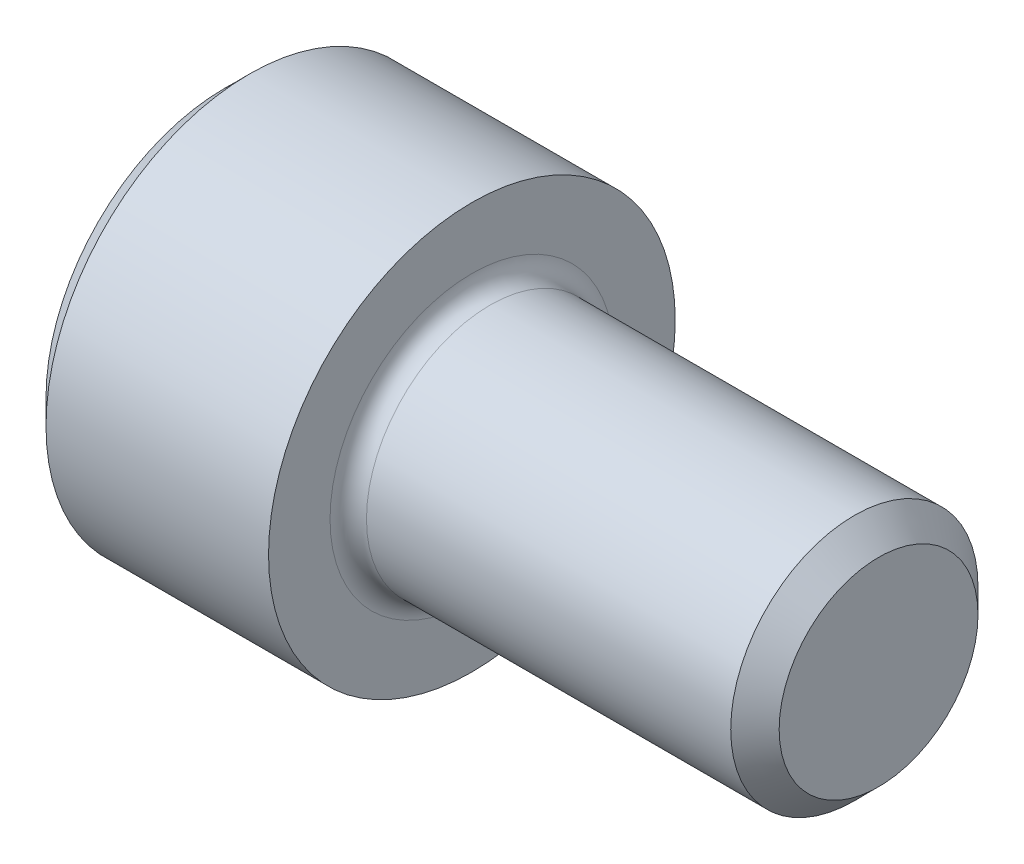
SolidWorks part; units mm, degrees
revolve "Base-Revolve" add sketch "BodySke"
sketch "BodySke" plane through (0, 0, 0) normal (0, 0, 1) x (1, 0, 0)
  line L0 (0, 0) -> (0, 3.4862)
  line L1 (0.4826, 3.9688) -> (4.826, 3.9688)
  line L2 (4.826, 3.9688) -> (4.826, 2.413)
  line L3 (4.826, 2.413) -> (12.2911, 2.413)
  line L4 (12.7635, 1.9406) -> (12.7635, 0)
  line L5 (12.7635, 0) -> (0, 0)
  line L6 (-31.75, 0) -> (127, 0) construction
  line L7 (0, 3.4862) -> (0.4826, 3.9688)
  line L8 (12.7635, 1.9406) -> (12.2911, 2.413)
  line L9 (0, -3.4862) -> (0.4826, -3.9688) construction
  line L10 (12.7635, -1.9406) -> (12.2911, -2.413) construction
  line L11 (5.6185, 9.525) -> (5.6185, 3.175) construction
  line L12 (4.826, 9.525) -> (4.826, 3.175) construction
  line L13 (-25.3365, 9.525) -> (-25.3365, 3.175) construction
  dimension "Diameter" = 4.826
  dimension "Head_ht" = 4.826
  dimension "Length" = 7.9375
  dimension "Body_ch_ang" = 45
  dimension "Head_dia" = 7.9375
  dimension "Head_ch_ang" = 45
  dimension "Head_side_ht" = 4.3434
  dimension "Minor_dia" = 3.8811
  dimension "Advance" = 0.7925
  dimension "Thread_nom" = 7.9375
  dimension "Thread_length" = 38.1
cosmetic thread "ThreadCosmetic" [suppressed]
fillet "Fillet1" radius 0.3556 1 edges at (4.826, 0, 2.413)
material "Plastique personnalisé"
ref_plane "Plane1" through (0, 0, 0) normal (0, 0, 1) x (1, 0, 0)
ref_plane "Plane2" through (0, 0, 0) normal (0, 1, 0) x (1, 0, 0)
ref_plane "Plane3" through (0, 0, 0) normal (1, 0, 0) x (0, 0, -1)
sketch "Sketch2" plane through (0, 0, 0) normal (0, 0, 1) x (1, 0, 0)
  line L0 (0, 1.985) -> (2.286, 1.985)
  line L1 (2.286, 1.985) -> (3.432, 0)
  line L2 (-31.75, 0) -> (127, 0) construction
  line L3 (3.432, 0) -> (0, 0)
  line L4 (0, 0) -> (0, 1.985)
  line L5 (0, 3.4862) -> (0, -3.4862) construction
  line L6 (0, 0) -> (47.625, 0) construction
  line L7 (4.826, -3.9688) -> (4.826, 3.9688) construction
  dimension "D1" = 1.985
  dimension "D2" = 60
revolve "Hex-PreBroach" cut sketch "Sketch2" angle 360 about L6
sketch "Sketch3" plane through (0, 0, 0) normal (-1, 0, 0) x (0, 0.5, 0.866)
  line L0 (1.146, 1.985) -> (-1.146, 1.985)
  line L1 (-1.146, 1.985) -> (-2.2921, 0)
  line L2 (1.146, 1.985) -> (2.2921, 0)
  line L3 (1.146, -1.985) -> (2.2921, 0)
  line L4 (1.146, -1.985) -> (-1.146, -1.985)
  line L5 (-1.146, -1.985) -> (-2.2921, 0)
  dimension "D1" = 1.985
  dimension "D2" = 1.985
  dimension "Hex_size" = 3.97
extrude "Hex" cut sketch "Sketch3" against normal blind 2.286
sketch "Sketch4" plane through (0, 0, 0) normal (-1, 0, 0) x (0, 0, 1)
  line L0 (0, 0) -> (2.3876, 0)
  line L1 (0, 0) -> (6.1484, 3.5498) construction
  line L2 (0, 0) -> (1.1938, 2.0677)
  line L3 (1.9883, 0.576) -> (2.2704, 0.7389)
  line L4 (1.493, 1.4339) -> (1.7751, 1.5968)
  arc A0 (1.9883, 0.576) -> (1.493, 1.4339) centre (0, 0) ccw
  arc A1 (2.3876, 0) -> (2.2704, 0.7389) centre (0, 0) ccw
  arc A2 (1.1938, 2.0677) -> (1.7751, 1.5968) centre (0, 0) cw
  dimension "D1" = 30
  dimension "D2" = 60
  dimension "Spline_p_dim" = 0.9906
  dimension "D3" = 0.4953
extrude "Spline" [suppressed] cut sketch "Sketch4" against normal blind 2.286
pattern_circular "CirPattern1" [suppressed] count 6 every 60
sketch "Sketch5" plane through (0, 0, 0) normal (0, 0, 1) x (1, 0, 0)
  line L0 (-31.75, 0) -> (127, 0) construction
  line L2 (0, 3.4862) -> (0, -3.4862) construction
  circle A0 centre (1.651, 0) radius 0.5906
  dimension "Drilled_hole_dia" = 1.1811
  dimension "Drilled_hole_loc" = 1.651
extrude "Hole" [suppressed] cut sketch "Sketch5" against normal through all and the other way through all
pattern_circular "Drilled-4" [suppressed] count 2 every 60
pattern_circular "Drilled-6" [suppressed] count 3 every 60
sketch "ThdSchSke" plane through (0, 0, 0) normal (0, 0, 1) x (1, 0, 0)
  line L0 (5.6185, -1.9406) -> (5.2877, -2.413)
  line L1 (5.6185, -1.9406) -> (5.9493, -2.413)
  line L2 (5.9493, -2.413) -> (5.9493, -3.0162)
  line L3 (-3.175, 0) -> (5.1513, 0) construction
  line L5 (5.9493, -3.0162) -> (5.2877, -3.0162)
  line L6 (5.2877, -3.0162) -> (5.2877, -2.413)
  line L7 (0, 3.4862) -> (0, -3.4862) construction
  dimension "Thread_minor" = 3.8811
  dimension "Diameter" = 4.826
  dimension "Start" = 5.6185
revolve "ThreadSchematic" [suppressed] cut sketch "ThdSchSke" angle 360 about L3
pattern_linear "ThdSchPat" [suppressed]
equation "\"D2@Sketch3\" = \"Hex_size@Sketch3\" / 2"
equation "\"D1@Sketch3\" = \"Hex_size@Sketch3\" / 2"
equation "\"D1@Sketch2\" = \"Hex_size@Sketch3\" / 2"
equation "\"D3@Sketch4\" = \"Spline_p_dim@Sketch4\" / 2"
equation "\"Thread_minor@ThreadCosmetic\"  =  \"Minor_dia@BodySke\""
equation "\"D2@CirPattern1\" = 360 / \"Num_teeth@CirPattern1\""
equation "\"Wall_thickness@Sketch2\" = \"Head_ht@BodySke\" - \"Key_eng@Hex\""
equation "\"Thread_length@ThreadCosmetic\" = ((sgn( (\"Length@BodySke\" - \"Advance@BodySke\" ) - \"Thread_nom@BodySke\" )-1)*( (\"Length@BodySke\" - \"Advance@BodySke\" ) - \"Thread_nom@BodySke\" ))/-2+ \"Thread_nom@BodySke\""
equation "\"Thread_minor@ThdSchSke\" = \"Minor_dia@BodySke\""
equation "\"Diameter@ThdSchSke\" = \"Diameter@BodySke\""
equation "\"Overcut@ThdSchSke\" = \"Diameter@BodySke\" * 1.25"
equation "\"Start@ThdSchSke\" = \"Head_ht@BodySke\" + \"Length@BodySke\" - \"Thread_length@ThreadCosmetic\"  '---Non-countersunk---"
equation "\"Num_threads@ThdSchPat\" = int( \"Thread_length@ThreadCosmetic\" / \"Advance@BodySke\" + 0.999 )  + 1"
equation "\"Advance@ThdSchPat\" = \"Thread_length@ThreadCosmetic\" /  (\"Num_threads@ThdSchPat\" - 1) 'relax it"
equation "\"Num_threads@ThdSchPat\" = \"Num_threads@ThdSchPat\" - sgn( \"Num_threads@ThdSchPat\" - 1) '---chamfered tips only---"
